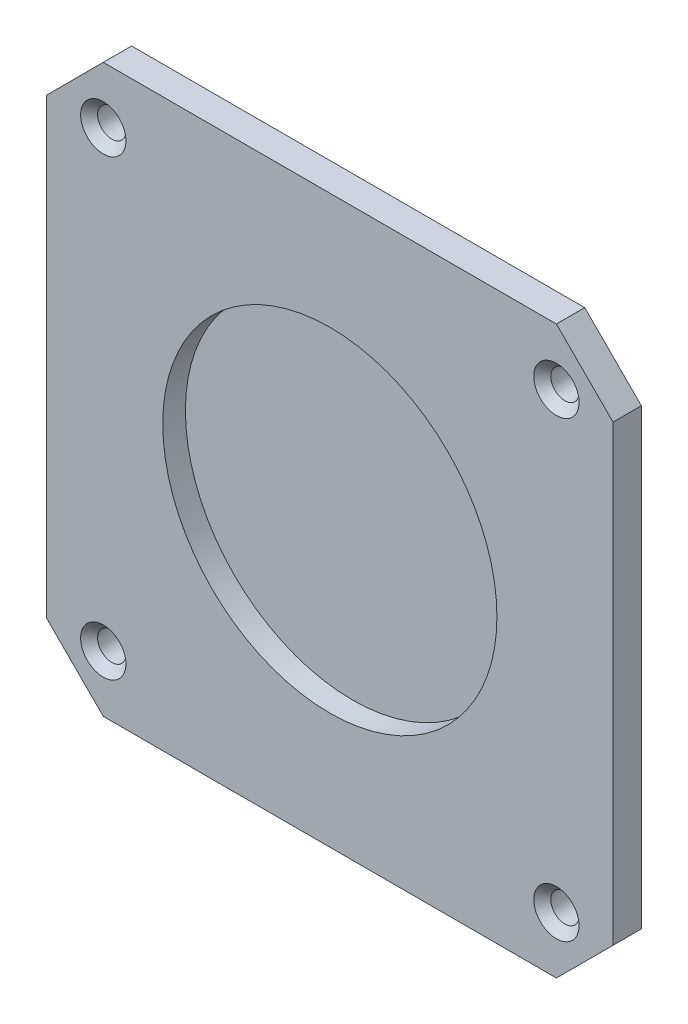
SolidWorks part; units mm, degrees
ref_plane "Front Plane" through (0, 0, 0) normal (0, 0, 1) x (1, 0, 0)
ref_plane "Top Plane" through (0, 0, 0) normal (0, 1, 0) x (1, 0, 0)
ref_plane "Right Plane" through (0, 0, 0) normal (1, 0, 0) x (0, 0, -1)
sketch "base" plane through (0, 0, 0) normal (0, 0, 1) x (1, 0, 0)
  line L21 (0, 10) -> (0, 90)
  line L22 (10, 0) -> (90, 0)
  line L24 (0, 90) -> (10, 100)
  line L25 (0, 10) -> (10, 0)
  line L27 (90, 0) -> (100, 10)
  line L28 (100, 10) -> (100, 90)
  line L29 (100, 90) -> (90, 100)
  line L30 (90, 100) -> (10, 100)
  dimension "D1" = 80
  dimension "D3" = 100
extrude "Boss-Extrude1" add sketch "base" along normal blind 5
sketch "circle" plane through (0, 0, 5) normal (0, 0, 1) x (1, 0, 0)
  line L0 (90, 100) -> (10, 100) construction
  line L1 (50, 100) -> (50, 0) construction
  line L2 (10, 0) -> (90, 0) construction
  circle A0 centre (50, 50) radius 29.5
  dimension "D1" = 59
extrude "Cut-Extrude1" cut sketch "circle" against normal blind 4
hole_wizard "CSK for M4 SFHCS1" positions "Sketch2" profile "Sketch3" countersink size "M4" standard "ANSI Metric" end condition through all
sketch "Sketch2" plane through (0, 0, 5) normal (0, 0, 1) x (1, 0, 0)
  line L0 (10, 0) -> (10, 100) construction
  line L2 (0, 10) -> (100, 10) construction
  line L4 (90, 100) -> (90, 0) construction
  line L6 (0, 90) -> (100, 90) construction
  point P25 (10, 90)
  point P27 (10, 10)
  point P29 (90, 10)
  point P31 (90, 90)
sketch "Sketch3" plane through (90, 90, 5) normal (1, 0, 0) x (0, -1, 0)
  line L0 (0, 0) -> (0, 5)
  line L1 (0, 5) -> (2.5, 5)
  line L2 (2.5, 5) -> (2.5, 1.5)
  line L3 (2.5, 1.5) -> (4, 0)
  line L5 (4, 0) -> (0, 0)
  line L6 (-2.5, 1.5) -> (-4, 0) construction
  line L11 (0, -6.35) -> (0, 107.95) construction
  dimension "Thru Hole Dia." = 5
  dimension "Thru Hole Depth" = 5
  dimension "Near C'Sink Dia." = 8
  dimension "Near C'Sink Angle" = 90
